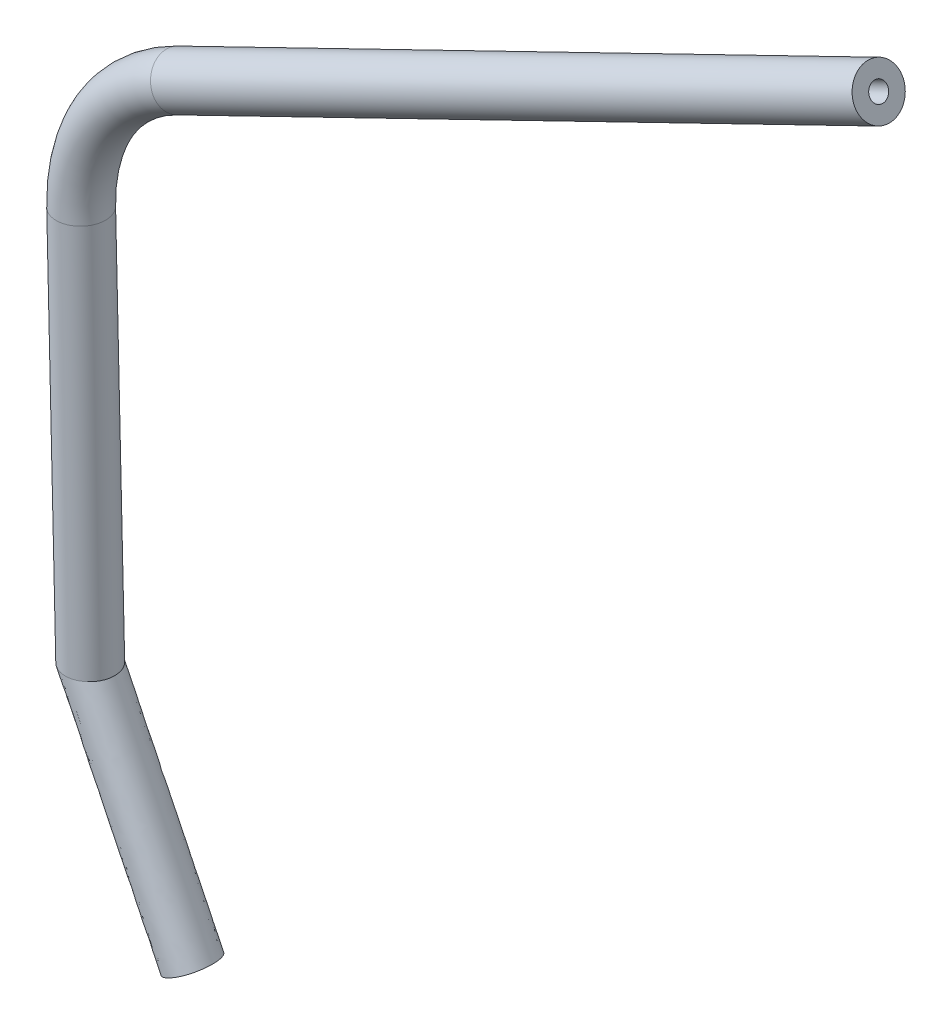
SolidWorks part; units mm, degrees
material "Cast Carbon Steel"
ref_plane "Front Plane" through (0, 0, 0) normal (0, 0, 1) x (1, 0, 0)
ref_plane "Top Plane" through (0, 0, 0) normal (0, 1, 0) x (1, 0, 0)
ref_plane "Right Plane" through (0, 0, 0) normal (1, 0, 0) x (0, 0, -1)
sketch "Sketch4" plane through (0, 0, 0) normal (0, 0, 1) x (1, 0, 0)
  arc A0 (-38.8747, 79.9498) -> (-88.8758, -2.0729) centre (0, 0) ccw
  dimension "D1" = 88.9
  dimension "D2" = 38.8747
  dimension "D3" = 88.8758
sketch "Sketch5" plane through (0, 0, 0) normal (0, 1, 0) x (1, 0, 0)
  circle A0 centre (-88.8758, 0) radius 12.7
  circle A1 centre (-88.8758, 0) radius 4.7625
  dimension "D1" = 25.4
  dimension "D2" = 7.9375
sweep "Sweep1" add profiles "Sketch5" path "Sketch4"
ref_plane "Plane4" through (0, 0, 0) normal (0.8993, 0.4373, 0) x (0, 0, -1)
sketch "Sketch6" plane through (0, 0, 0) normal (0.8993, 0.4373, 0) x (0, 0, -1)
  circle A0 centre (0, 88.8758) radius 12.7
  circle A1 centre (0, 88.8758) radius 4.7625
  dimension "D1" = 7.9375
  dimension "D2" = 9.525
  dimension "D3" = 88.8758
extrude "Boss-Extrude3" add sketch "Sketch6" along normal blind 406.4
ref_plane "Plane5" through (0, 0, 0) normal (0.0233, -0.9997, 0) x (-0.9997, -0.0233, 0)
sketch "Sketch7" plane through (0, 0, 0) normal (0.0233, -0.9997, 0) x (-0.9997, -0.0233, 0)
  circle A0 centre (88.8758, 0) radius 12.7
  circle A1 centre (88.8758, 0) radius 4.7625
  dimension "D1" = 7.9375
  dimension "D2" = 25.4
  dimension "D3" = 88.8758
extrude "Boss-Extrude4" add sketch "Sketch7" along normal blind 203.2
ref_plane "Plane7" through (0, 0, -12.7) normal (0, 0, -1) x (-1, 0, 0)
sketch "Sketch9" plane through (0, 0, -12.7) normal (0, 0, -1) x (-1, 0, 0)
  line L0 (33.3106, 68.5067) -> (44.4176, 91.3495) construction
  line L1 (76.1551, -1.7762) -> (101.5482, -2.3685) construction
  circle A0 centre (76.2699, 46.4942) radius 12.7
  dimension "D1" = 25.4
  dimension "D2" = 48.26
  dimension "D3" = 48.26
extrude "Cut-Extrude2" cut sketch "Sketch9" against normal blind 6.35
ref_plane "Plane8" through (4.7381, -203.1448, 0) normal (0.0233, -0.9997, 0) x (-0.9997, -0.0233, 0)
sketch "Sketch10" plane through (4.7381, -203.1448, 0) normal (0.0233, -0.9997, 0) x (-0.9997, -0.0233, 0)
  circle A0 centre (88.8758, 0) radius 12.7
  circle A1 centre (88.8758, 0) radius 4.7625
  circle A2 centre (88.8758, 0) radius 12.7 construction
  dimension "D1" = 7.9375
  dimension "D2" = 9.525
sketch "Sketch11" plane through (0, 0, 0) normal (0, 0, 1) x (1, 0, 0)
  line L0 (-84.1136, -205.2171) -> (-28.5784, -319.4311)
  line L1 (24.0507, -49.4628) -> (-24.0507, 49.4628) construction
  dimension "D1" = 127
sweep "Sweep2" add profiles "Sketch10" path "Sketch11"
sketch "Sketch12" plane through (0, 0, 0) normal (0, 0, 1) x (1, 0, 0)
  line L0 (-41.2749, -319.7272) -> (-20.5045, -309.6279)
  line L1 (-15.8818, -319.135) -> (-71.417, -204.921) construction
  line L2 (-20.5045, -309.6279) -> (-15.8818, -319.135)
  line L3 (-15.8818, -319.135) -> (-41.2749, -319.7272)
extrude "Cut-Extrude3" cut sketch "Sketch12" against normal through all both and the other way through all
